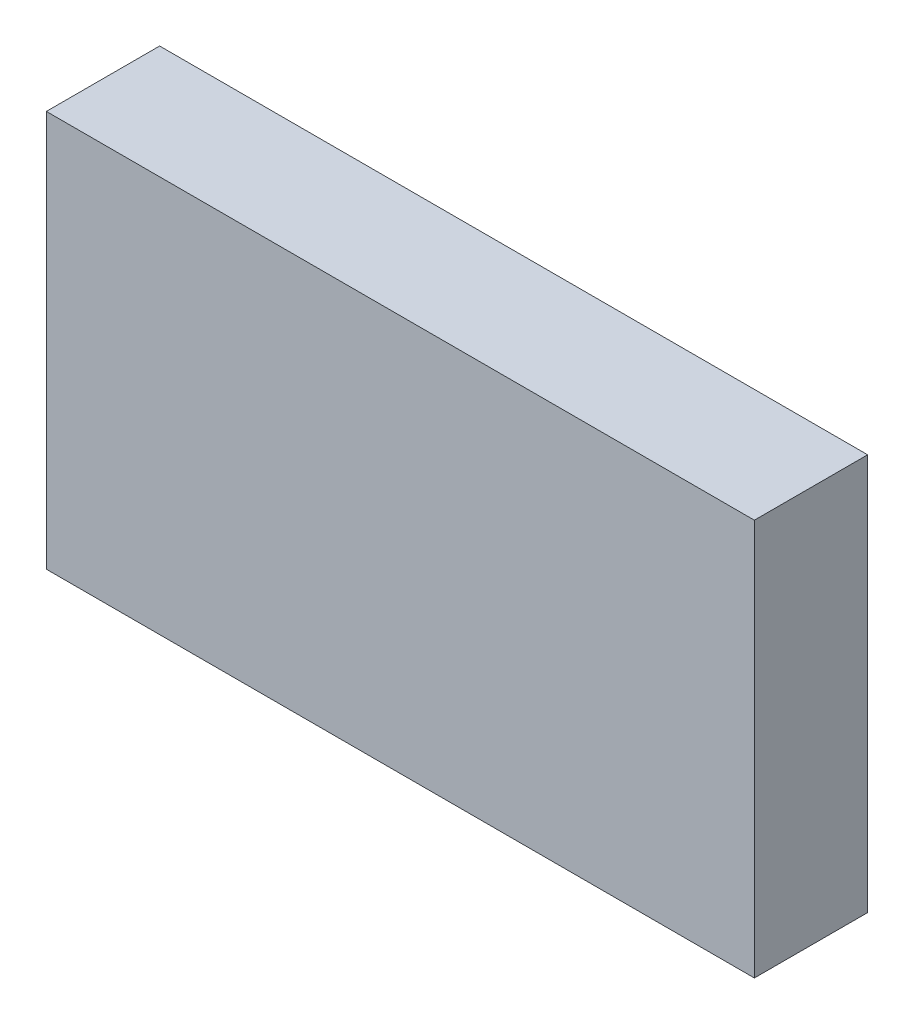
SolidWorks part; units mm, degrees
ref_plane "Спереди" through (0, 0, 0) normal (0, 0, 1) x (1, 0, 0)
ref_plane "Сверху" through (0, 0, 0) normal (0, 1, 0) x (1, 0, 0)
ref_plane "Справа" through (0, 0, 0) normal (1, 0, 0) x (0, 0, -1)
sketch "Эскиз1" plane through (0, 0, 0) normal (0, 0, 1) x (1, 0, 0)
  line L1 (0, 0) -> (12.5, 0)
  line L2 (0, 0) -> (0, 7)
  line L3 (0, 7) -> (12.5, 7)
  line L4 (12.5, 0) -> (12.5, 7)
  dimension "D1" = 12.5
  dimension "D2" = 7
extrude "Бобышка-Вытянуть1" add sketch "Эскиз1" along normal blind 2
